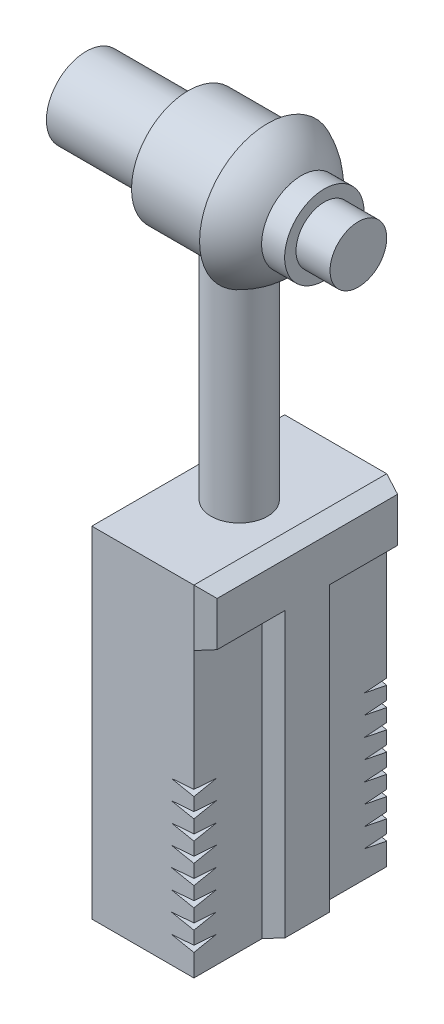
SolidWorks part; units mm, degrees
ref_plane "Front Plane" through (0, 0, 0) normal (0, 0, 1) x (1, 0, 0)
ref_plane "Top Plane" through (0, 0, 0) normal (0, 1, 0) x (1, 0, 0)
ref_plane "Right Plane" through (0, 0, 0) normal (1, 0, 0) x (0, 0, -1)
sketch "Sketch2" plane through (0, 0, 0) normal (1, 0, 0) x (0, 0, -1)
  line L0 (-8.5, 15) -> (8.5, 15)
  line L1 (8.5, 15) -> (8.5, -15)
  line L2 (8.5, -15) -> (-8.5, -15)
  line L3 (-8.5, -15) -> (-8.5, 15)
  point P2 (0, 15)
  point P5 (-8.5, 0)
  dimension "D1" = 30
  dimension "D2" = 17
extrude "Boss-Extrude1" add sketch "Sketch2" along normal mid plane 9 contours L3 L0 L1 L2
shell "Shell1" thickness 0.75
sketch "Sketch12" plane through (0, 0, 8.5) normal (0, 0, 1) x (1, 0, 0)
  line L0 (4.5, -12.5) -> (2.5, -12.65)
  line L2 (2.5, -12.65) -> (4.5, -13.05)
  line L3 (4.5, -13.05) -> (4.5, -12.5)
  line L4 (4.5, -15) -> (4.5, 15) construction
  dimension "D1" = 2
  dimension "D2" = 0.15
  dimension "D3" = 2.5
  dimension "D4" = 0.4
revolve "Cut-Revolve1" cut sketch "Sketch12" angle 360 about axis through (4.5, -15, 8.5) along (0, 1, 0)
pattern_linear "LPattern1" count 8 spacing 1.7 along (0, 1, 0) of "Cut-Revolve1"
ref_plane "Plane1" through (0, 39, 0) normal (0, 1, 0) x (1, 0, 0)
sketch "Sketch5" plane through (0, 39, 0) normal (0, 1, 0) x (1, 0, 0)
  line L0 (16.7499, 0) -> (-3.7499, 0) construction
  line L1 (2.5, 0) -> (2.5, -6) construction
  line L2 (2.5, 0) -> (2.5, 6)
  line L3 (2.5, 0) -> (6.5, 0)
  arc A0 (2.5, 6) -> (6.5, 0) centre (0, 0) cw
  arc A1 (6.5, 0) -> (2.5, -6) centre (0, 0) cw construction
  dimension "D1" = 12
  dimension "D2" = 6.5
  dimension "D3" = 2.5
revolve "Revolve1" add sketch "Sketch5" angle 360 about L0
sketch "Sketch7" plane through (2.5, 0, 0) normal (-1, 0, 0) x (0, 0, 1)
  circle A0 centre (0, 39) radius 5
  circle A1 centre (0, 39) radius 6 construction
  dimension "D1" = 10
extrude "Boss-Extrude3" add sketch "Sketch7" along normal up to surface (7 mm away) up to face at (-4.5, 0, 0)
sketch "Sketch3" plane through (0, 15, 0) normal (0, 1, 0) x (1, 0, 0)
  circle A0 centre (0, 0) radius 2.5
  dimension "D1" = 5
extrude "Boss-Extrude2" add sketch "Sketch3" along normal up to surface (19.6699 mm away)
sketch "Sketch8" plane through (-4.5, 0, 0) normal (-1, 0, 0) x (0, 0, 1)
  circle A0 centre (0, 39) radius 3.5
  dimension "D1" = 7
extrude "Boss-Extrude4" add sketch "Sketch8" along normal blind 9
sketch "Sketch9" plane through (2.5, 0, 0) normal (1, 0, 0) x (0, 0, -1)
  circle A0 centre (0, 39) radius 3.5
  dimension "D1" = 7
extrude "Boss-Extrude5" add sketch "Sketch9" along normal blind 5 contours A0
sketch "Sketch11" plane through (7.5, 0, 0) normal (1, 0, 0) x (0, 0, -1)
  circle A0 centre (0, 39) radius 2.5
  dimension "D1" = 5
extrude "Boss-Extrude6" add sketch "Sketch11" along normal blind 3
sketch "Sketch13" plane through (4.5, 0, 0) normal (1, 0, 0) x (0, 0, -1)
  line L0 (-8.5, 15) -> (-8.5, 10)
  line L1 (-8.5, -0.6) -> (-8.5, 15) construction
  line L2 (-8.5, 10) -> (-2.5, 10)
  line L3 (-2.5, 10) -> (-2.5, -15)
  line L4 (8.5, -15) -> (-8.5, -15) construction
  line L5 (-2.5, -15) -> (2.5, -15)
  line L6 (2.5, -15) -> (2.5, 10)
  line L7 (2.5, 10) -> (8.5, 10)
  line L8 (8.5, 15) -> (8.5, -15) construction
  line L9 (8.5, 10) -> (8.5, 15)
  line L10 (8.5, 15) -> (-8.5, 15)
  point P10 (0, -15)
  dimension "D1" = 5
  dimension "D2" = 5
extrude "Boss-Extrude7" add sketch "Sketch13" along normal blind 1.5 draft 20
mirror "Mirror1" about plane through (0, 0, 0) normal (0, 0, 1) of "Cut-Revolve1", "LPattern1"
